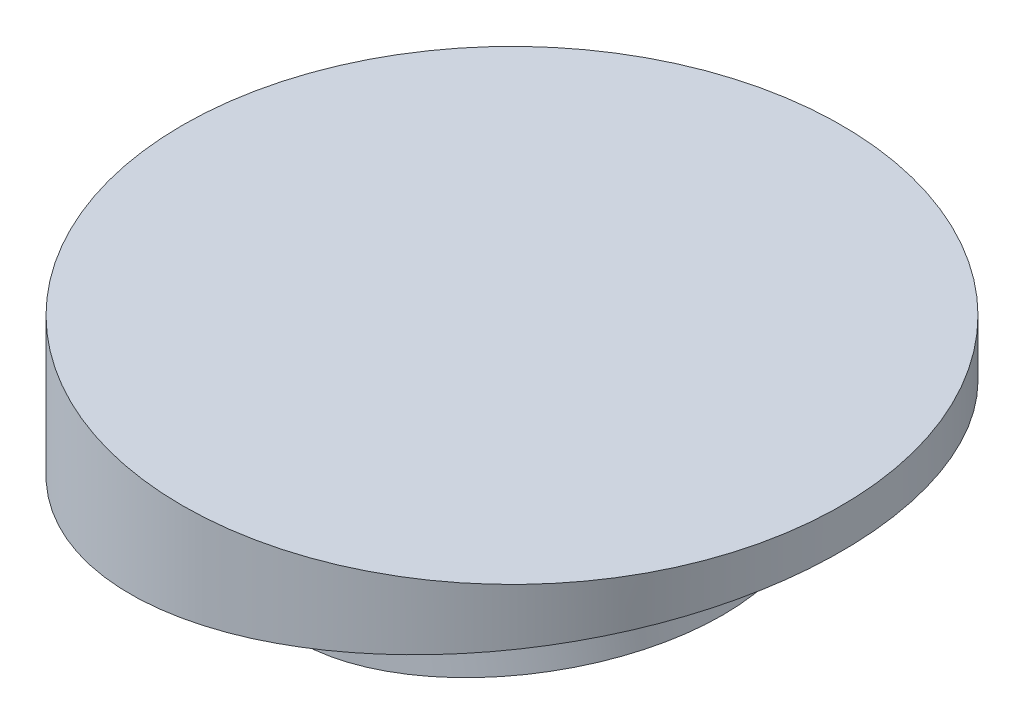
SolidWorks part; units mm, degrees
material "ABS"
ref_plane "前视基准面" through (0, 0, 0) normal (0, 0, 1) x (1, 0, 0)
ref_plane "上视基准面" through (0, 0, 0) normal (0, 1, 0) x (1, 0, 0)
ref_plane "右视基准面" through (0, 0, 0) normal (1, 0, 0) x (0, 0, -1)
sketch "草图5" plane through (0, 0, 0) normal (0, 1, 0) x (1, 0, 0)
  circle A0 centre (0, 0) radius 25
  dimension "D1" = 50
extrude "凸台-拉伸4" add sketch "草图5" along normal blind 20
sketch "草图7" plane through (0, 0, 0) normal (0, 0, 1) x (1, 0, 0)
  line L0 (-25, 8.1837) -> (25, 17)
  line L1 (-25, 20) -> (-25, 0) construction
  line L2 (25, 0) -> (25, 20) construction
  line L3 (25, 17) -> (25, -9.7273)
  line L4 (25, -9.7273) -> (-25, -9.7273)
  line L5 (-25, -9.7273) -> (-25, 8.1837)
  line L6 (-25, 0) -> (25, 0) construction
  line L7 (25, 20) -> (-25, 20) construction
  dimension "D1" = 10
  dimension "D2" = 3
extrude "切除-拉伸2" cut sketch "草图7" against normal mid plane 82
sketch "草图8" plane through (-2.1533, 12.2121, 0) normal (0.1736, -0.9848, 0) x (0.9848, 0.1736, 0)
  circle A0 centre (2.1865, 0) radius 15
  dimension "D1" = 30
extrude "凸台-拉伸5" add sketch "草图8" along normal blind 7
